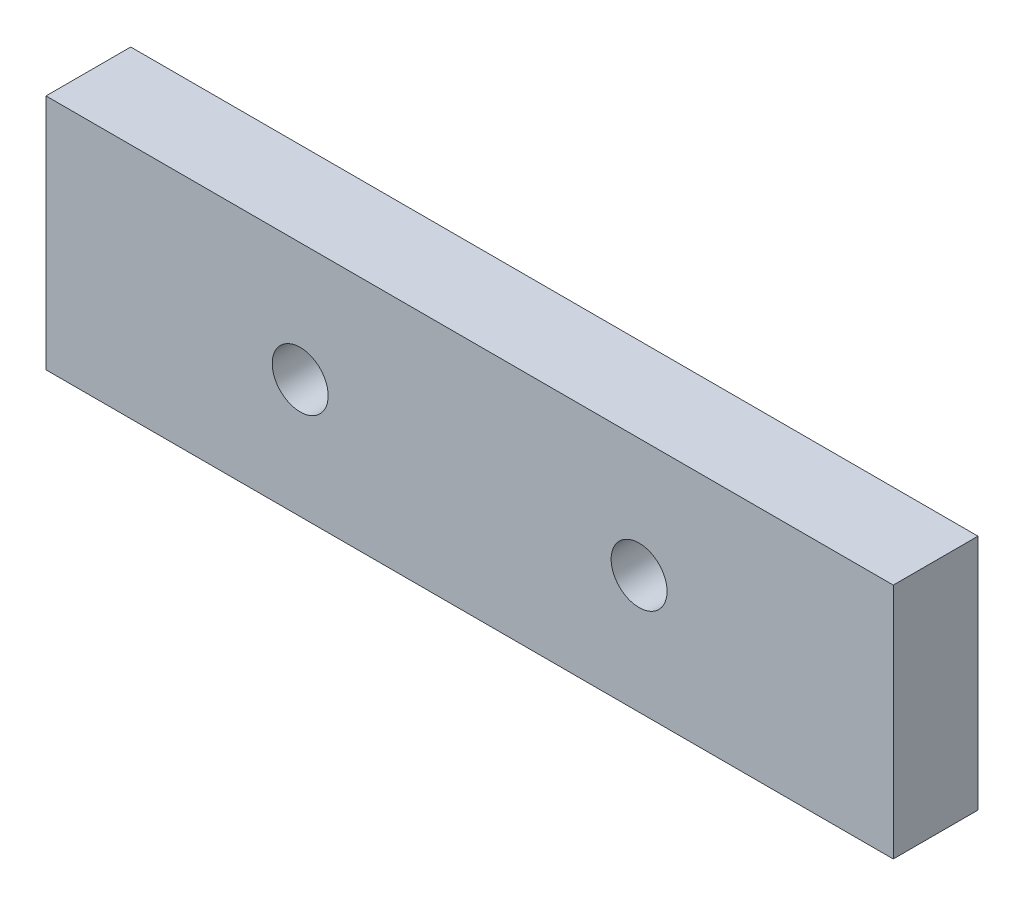
SolidWorks part; units mm, degrees
ref_plane "Front Plane" through (0, 0, 0) normal (0, 0, 1) x (1, 0, 0)
ref_plane "Top Plane" through (0, 0, 0) normal (0, 1, 0) x (1, 0, 0)
ref_plane "Right Plane" through (0, 0, 0) normal (1, 0, 0) x (0, 0, -1)
sketch "Sketch1" plane through (0, 0, 0) normal (0, 0, 1) x (1, 0, 0)
  line L1 (-25, -7) -> (25, -7)
  line L2 (-25, -7) -> (-25, 7)
  line L3 (-25, 7) -> (25, 7)
  line L4 (25, -7) -> (25, 7)
  line L5 (-25, -7) -> (25, 7) construction
  line L6 (-25, 7) -> (25, -7) construction
  point P0 (0, 0)
  dimension "D1" = 50
  dimension "D2" = 14
extrude "Boss-Extrude1" add sketch "Sketch1" along normal mid plane 5
hole_wizard "M4x0.7 Tapped Hole1" positions "Sketch2" profile "Sketch3" tap size "M4x0.7" standard "ANSI Metric" end condition through all
sketch "Sketch2" plane through (0, 0, 2.5) normal (0, 0, 1) x (1, 0, 0)
  line L0 (-25, 7) -> (-25, -7) construction
  line L1 (-25, 7) -> (-25, -7) construction
  point P0 (-10, 0)
  point P2 (10, 0)
  point P13 (-25, 0)
  dimension "D1" = 20
  dimension "D2" = 15
sketch "Sketch3" plane through (-10, 0, 2.5) normal (1, 0, 0) x (0, -1, 0)
  line L0 (0, 0) -> (0, 5)
  line L1 (0, 5) -> (1.65, 5)
  line L2 (1.65, 5) -> (1.65, 0)
  line L5 (1.65, 0) -> (0, 0)
  line L11 (0, -6.35) -> (0, 107.95) construction
  dimension "Thru Tap Drill Dia." = 3.3
  dimension "Thru Tap Drill Depth" = 5
cosmetic thread "Hole Thread1"
cosmetic thread "Hole Thread2"
